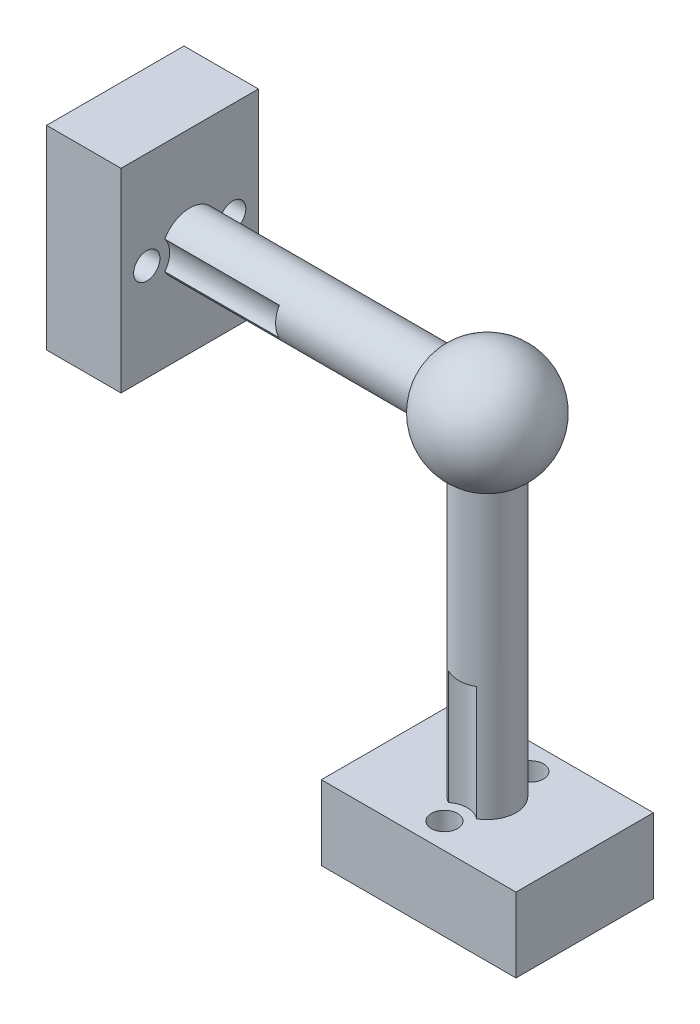
SolidWorks part; units mm, degrees
ref_plane "정면" through (0, 0, 0) normal (0, 0, 1) x (1, 0, 0)
ref_plane "윗면" through (0, 0, 0) normal (0, 1, 0) x (1, 0, 0)
ref_plane "우측면" through (0, 0, 0) normal (1, 0, 0) x (0, 0, -1)
sketch "스케치1" plane through (0, 0, 0) normal (0, 0, 1) x (1, 0, 0)
  line L0 (0, 7.6428) -> (0, -7.5287) construction
  line L1 (0, -5) -> (0, 5)
  arc A0 (0, 5) -> (0, -5) centre (0, 0) ccw
  point P5 (0, -7.5287)
  dimension "D1" = 5
revolve "회전1" add sketch "스케치1" angle 360 about L0
sketch "스케치2" plane through (0, 0, 0) normal (0, 1, 0) x (1, 0, 0)
  circle A0 centre (0, 0) radius 2.5
  dimension "D1" = 5
extrude "보스-돌출1" add sketch "스케치2" against normal blind 29
ref_plane "평면1" through (0, -35.5, 0) normal (0, -1, 0) x (-1, 0, 0)
sketch "스케치3" plane through (0, 0, 0) normal (1, 0, 0) x (0, 0, -1)
  circle A0 centre (0, 0) radius 2.5
  dimension "D1" = 5
extrude "보스-돌출2" add sketch "스케치3" against normal blind 26
ref_plane "평면2" through (-32.5, 0, 0) normal (1, 0, 0) x (0, 0, -1)
sketch "스케치5" plane through (0, -35.5, 0) normal (0, -1, 0) x (-1, 0, 0)
  line L0 (0, 5.5) -> (0, -5.5) construction
  line L1 (-8.5, 6) -> (8.5, 6)
  line L2 (-8.5, 6) -> (-8.5, -6)
  line L3 (-8.5, -6) -> (8.5, -6)
  line L4 (8.5, 6) -> (8.5, -6)
  circle A0 centre (0, 3.75) radius 1.15
  circle A1 centre (0, -3.75) radius 1.15
  dimension "D5" = 7.5
  dimension "D7" = 2.3
  dimension "D1" = 12
  dimension "D2" = 17
  dimension "D3" = 6
  dimension "D4" = 8.5
  dimension "D6" = 3.75
extrude "보스-돌출4" add sketch "스케치5" against normal blind 6.5
sketch "스케치6" plane through (0, -29, 0) normal (0, 1, 0) x (1, 0, 0)
  circle A0 centre (0, 3.75) radius 2
  circle A1 centre (0, -3.75) radius 2
  circle A2 centre (0, 3.75) radius 1.15 construction
  circle A3 centre (0, -3.75) radius 1.15 construction
  point P4 (0, 0)
  point P6 (0, 0)
  point P10 (0, 0)
  dimension "D1" = 4
extrude "컷-돌출1" cut sketch "스케치6" along normal blind 10
sketch "스케치7" plane through (-32.5, 0, 0) normal (1, 0, 0) x (0, 0, -1)
  line L0 (6.6, 0) -> (-6.6, 0) construction
  line L1 (6, -8.5) -> (-6, -8.5)
  line L2 (6, -8.5) -> (6, 8.5)
  line L3 (6, 8.5) -> (-6, 8.5)
  line L4 (-6, -8.5) -> (-6, 8.5)
  circle A0 centre (-3.75, 0) radius 1.15
  circle A1 centre (3.75, 0) radius 1.15
  dimension "D7" = 2.3
  dimension "D1" = 17
  dimension "D2" = 12
  dimension "D3" = 6
  dimension "D4" = 8.5
  dimension "D5" = 7.5
  dimension "D6" = 3.75
extrude "보스-돌출5" add sketch "스케치7" along normal blind 6.5
sketch "스케치8" plane through (-26, 0, 0) normal (1, 0, 0) x (0, 0, -1)
  circle A0 centre (-3.75, 0) radius 2
  circle A1 centre (3.75, 0) radius 2
  circle A2 centre (3.75, 0) radius 1.15 construction
  circle A3 centre (-3.75, 0) radius 1.15 construction
  point P4 (0, 0)
  point P7 (0, 0)
  dimension "D1" = 4
  dimension "D2" = 4
extrude "컷-돌출2" cut sketch "스케치8" along normal blind 10
